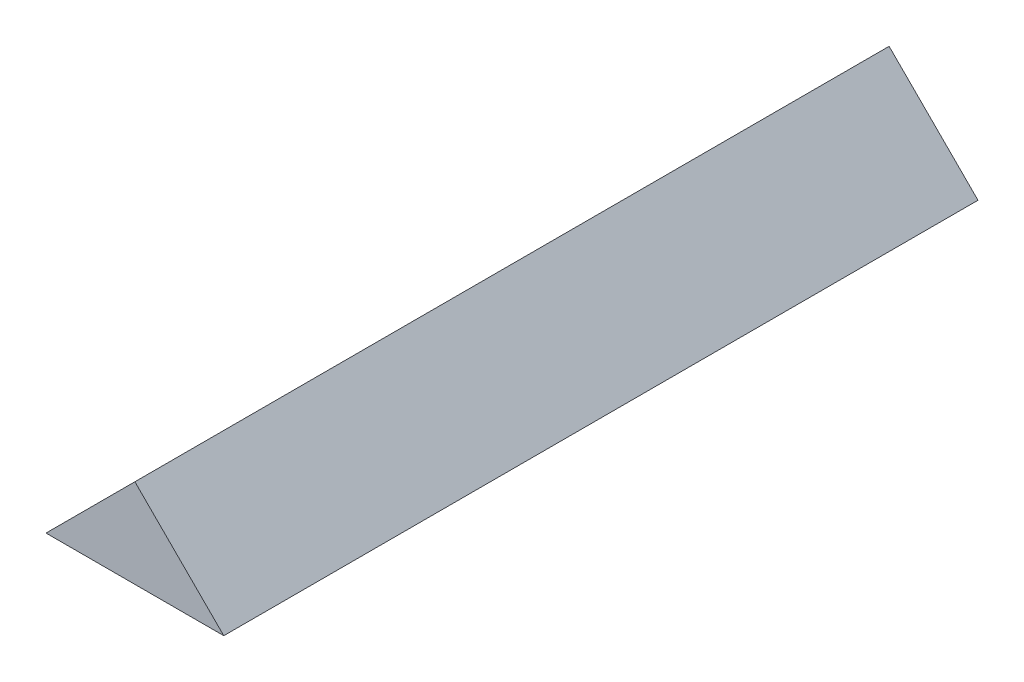
SolidWorks part; units mm, degrees
ref_plane "Front Plane" through (0, 0, 0) normal (0, 0, 1) x (1, 0, 0)
ref_plane "Top Plane" through (0, 0, 0) normal (0, 1, 0) x (1, 0, 0)
ref_plane "Right Plane" through (0, 0, 0) normal (1, 0, 0) x (0, 0, -1)
sketch "Sketch1" plane through (0, 0, 0) normal (0, 0, 1) x (1, 0, 0)
  line L0 (0, 0) -> (-35.3553, 0)
  line L1 (-35.3553, 0) -> (-17.6777, 17.6777)
  line L2 (-17.6777, 17.6777) -> (0, 0)
  dimension "D1" = 25
  dimension "D2" = 25
  dimension "D3" = 90
extrude "Boss-Extrude1" add sketch "Sketch1" along normal blind 150
